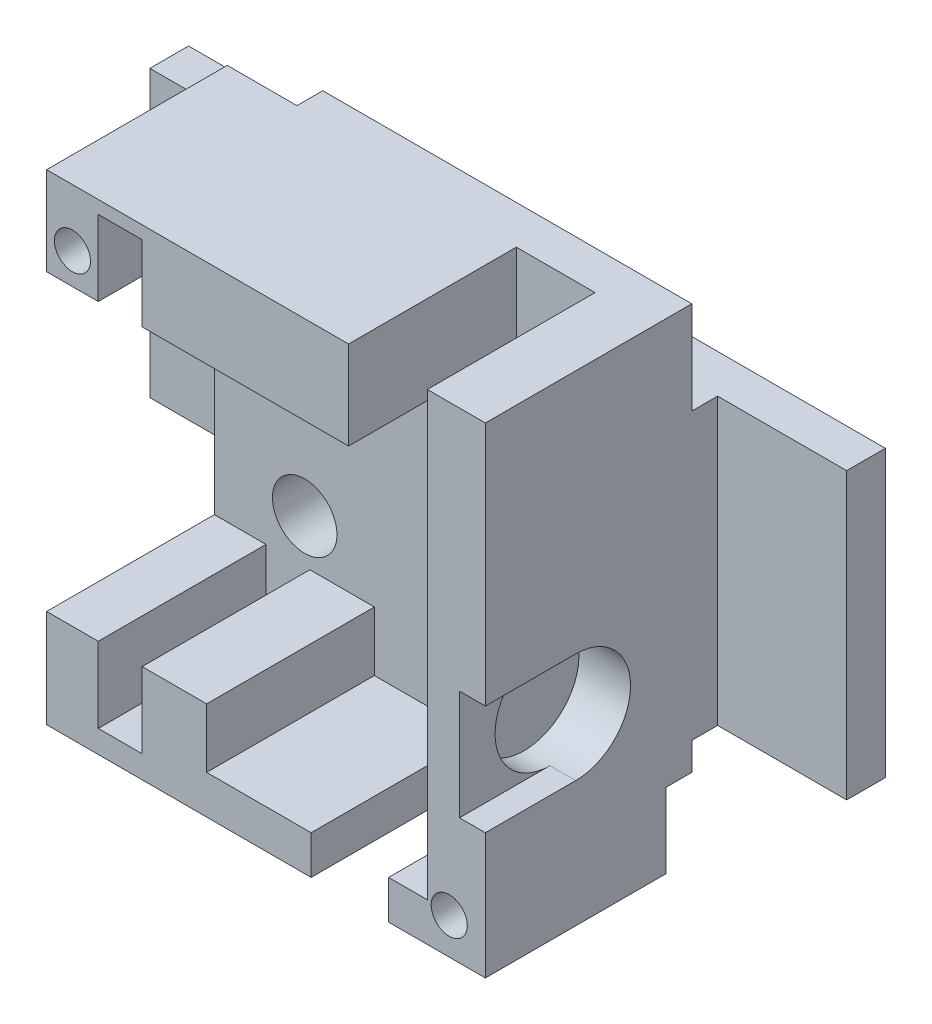
SolidWorks part; units mm, degrees
ref_plane "Front Plane" through (0, 0, 0) normal (0, 0, 1) x (1, 0, 0)
ref_plane "Top Plane" through (0, 0, 0) normal (0, 1, 0) x (1, 0, 0)
ref_plane "Right Plane" through (0, 0, 0) normal (1, 0, 0) x (0, 0, -1)
sketch "Sketch1" plane through (0, 0, 0) normal (0, 0, 1) x (1, 0, 0)
  line L1 (-17, 19) -> (17, 19)
  line L2 (-17, 19) -> (-17, -19)
  line L3 (-17, -19) -> (17, -19)
  line L4 (17, 19) -> (17, -19)
  line L5 (-17, 19) -> (17, -19) construction
  line L6 (-17, -19) -> (17, 19) construction
  point P0 (0, 0)
  dimension "D1" = 38
  dimension "D2" = 34
extrude "Boss-Extrude1" add sketch "Sketch1" along normal blind 16
sketch "Sketch2" plane through (0, 0, 16) normal (0, 0, 1) x (1, 0, 0)
  line L0 (0, 0) -> (-17, 0) construction
  line L5 (-17, 11.4) -> (5.4, 11.4)
  line L6 (-17, 11.4) -> (-17, -11.4)
  line L7 (-17, -11.4) -> (5.4, -11.4)
  line L8 (5.4, 11.4) -> (5.4, -11.4)
  line L9 (-17, 11.4) -> (5.4, -11.4) construction
  line L10 (-17, -11.4) -> (5.4, 11.4) construction
  line L11 (-17, 19) -> (-17, -19) construction
  line L12 (-10.6, -11.4) -> (-10.6, -16.25)
  line L13 (-13, 11.4) -> (-10.6, 11.4)
  line L14 (-13, 11.4) -> (-13, 16.25)
  line L15 (-13, 16.25) -> (-10.6, 16.25)
  line L16 (-10.6, 11.4) -> (-10.6, 16.25)
  line L17 (-13, -11.4) -> (-13, -16.25)
  line L18 (-13, -16.25) -> (-10.6, -16.25)
  line L21 (-17, -11.4) -> (-17, 4.4)
  point P0 (-5.8, 0)
  dimension "D1" = 22.4
  dimension "D2" = 22.8
  dimension "D3" = 5.8
  dimension "D4" = 4
  dimension "D5" = 2.4
  dimension "D6" = 4.85
extrude "Cut-Extrude1" cut sketch "Sketch2" against normal blind 13 contours L8 L5 L6 L7 | L17 L18 L12 L7 | L5 L16 L15 L14
sketch "Sketch3" plane through (0, 0, 16) normal (0, 0, 1) x (1, 0, 0)
  line L1 (5.4, -11.4) -> (-4.6, -11.4)
  line L2 (5.4, -11.4) -> (5.4, -16)
  line L3 (5.4, -16) -> (-4.6, -16)
  line L4 (-4.6, -11.4) -> (-4.6, -16)
  line L5 (5.4, -16) -> (8.4, -16)
  line L6 (5.4, -16) -> (5.4, -11.4)
  line L7 (5.4, -11.4) -> (8.4, -11.4)
  line L8 (8.4, -16) -> (8.4, -11.4)
  line L10 (-17, -19) -> (17, -19) construction
  line L11 (17, 19) -> (-17, 19) construction
  line L12 (8.4, -16) -> (11.4, -16)
  line L13 (8.4, -16) -> (8.4, 19)
  line L14 (8.4, 19) -> (11.4, 19)
  line L15 (11.4, -16) -> (11.4, 19)
  line M11 (17, 19) -> (-17, 19)
  line M21 (5.4, -11.4) -> (-10.6, -11.4)
  dimension "D1" = 3
  dimension "D2" = 10
  dimension "D3" = 3
  dimension "D4" = 3
extrude "Cut-Extrude2" cut sketch "Sketch3" against normal blind 13 contours L12 L15 L13 L8 M11 | L4 L3 L2 M21 | L5 L8 L7 L2
sketch "Sketch4" plane through (0, 0, 16) normal (0, 0, 1) x (1, 0, 0)
  line L0 (-17, 19) -> (-17, 11.4) construction
  line L3 (-17, -19) -> (17, -19) construction
  line L4 (17, -19) -> (17, 19) construction
  line L5 (8.4, 19) -> (-17, 19) construction
  circle A0 centre (-15, 13.8) radius 1.4
  circle A1 centre (14.2, -16.2) radius 1.4
  dimension "D2" = 5.2
  dimension "D3" = 2.8
  dimension "D4" = 2.8
  dimension "D5" = 2.8
  dimension "D6" = 2.8
  dimension "D1" = 2
extrude "Cut-Extrude3" cut sketch "Sketch4" against normal through all
sketch "Sketch5" plane through (0, 0, 0) normal (0, 0, -1) x (-1, 0, 0)
  line L0 (-17, 19) -> (17, 19) construction
  line L1 (18.4, 13.8) -> (11.6, 13.8)
  line L2 (18.4, 13.8) -> (18.4, 19)
  line L3 (18.4, 19) -> (11.6, 19)
  line L4 (11.6, 13.8) -> (11.6, 19)
  line L5 (-17, -19) -> (-17, 19) construction
  line L6 (-14.2, -19.2) -> (-17, -19.2)
  line L7 (-14.2, -19.2) -> (-14.2, -13.2)
  line L8 (-14.2, -13.2) -> (-17, -13.2)
  line L9 (-17, -19.2) -> (-17, -13.2)
  line L11 (-14.2, -19.2) -> (-10.2, -19.2)
  line L12 (-14.2, -19.2) -> (-14.2, -13.2)
  line L13 (-14.2, -13.2) -> (-10.2, -13.2)
  line L14 (-10.2, -19.2) -> (-10.2, -13.2)
  circle A0 centre (15, 13.8) radius 3.4
  circle A1 centre (-14.2, -16.2) radius 3
  circle M1 centre (15, 13.8) radius 1.4
  circle M2 centre (-14.2, -16.2) radius 1.4
  line M3 (-17, 19) -> (-17, -19)
  line M4 (-17, -19) -> (17, -19)
  line M5 (17, -19) -> (17, 19)
  line M6 (17, 19) -> (-17, 19)
  dimension "D1" = 6.8
  dimension "D2" = 6
  dimension "D3" = 4
extrude "Cut-Extrude5" cut sketch "Sketch5" against normal blind 2 contours A1 L7 M4 M2 | L7 A1 L9 M4 M2 | A1 M3 M4 | A1 L8 M3 | L9 A1 | A1 L7 M4 | A1 L9 L6 M4 | L7 A1 M4 | A0 L2 L3 M5 | A0 L4 M5 M6 | A0 L1 M5 M1 | L1 A0 M5 | A0 L1 M5 | L1 A0 M5 M1 | A1 L14 L13 M4
sketch "Sketch7" plane through (0, 19, 0) normal (0, 1, 0) x (1, 0, 0)
  line L0 (17, -16) -> (17, 0) construction
  line L1 (-17, -16) -> (17, -16)
  line L2 (-17, -16) -> (-17, -15)
  line L3 (-17, -15) -> (17, -15)
  line L4 (17, -16) -> (17, -15)
  dimension "D1" = 1
extrude "Cut-Extrude6" cut sketch "Sketch7" against normal through all
sketch "Sketch9" plane through (0, 0, 15) normal (0, 0, 1) x (1, 0, 0)
  line L0 (8.4, 19) -> (-17, 19) construction
  line L1 (-9, 19) -> (17, 19)
  line L2 (-9, 19) -> (-9, 12.5)
  line L3 (-9, 12.5) -> (17, 12.5)
  line L4 (17, 19) -> (17, 12.5)
  line L5 (17, -19) -> (17, 19) construction
  line L6 (-17, -19) -> (-17, -11.4) construction
  line L7 (-17, -12.4) -> (-14, -12.4)
  line L8 (-17, -12.4) -> (-17, -19)
  line L9 (-17, -19) -> (-14, -19)
  line L10 (-14, -12.4) -> (-14, -19)
  line L11 (17, -19) -> (-17, -19) construction
  line L12 (-13, -16.25) -> (-10.6, -16.25) construction
  line L13 (-8.6, -19) -> (-5.6, -19)
  line L14 (-8.6, -19) -> (-8.6, -12.4)
  line L15 (-8.6, -12.4) -> (-5.6, -12.4)
  line L16 (-5.6, -19) -> (-5.6, -12.4)
  line L17 (-5.6, -19) -> (11.4, -19)
  line L18 (-5.6, -19) -> (-5.6, -17)
  line L19 (-5.6, -17) -> (11.4, -17)
  line L20 (11.4, -19) -> (11.4, -17)
  line L21 (-14, -19) -> (-8.6, -19)
  line L22 (-14, -19) -> (-14, -18.25)
  line L23 (-10.6, -11.4) -> (-4.6, -11.4) construction
  line L24 (-17, -11.4) -> (-13, -11.4) construction
  line L25 (-10.6, -11.4) -> (-10.6, -16.25) construction
  line L26 (-4.6, -11.4) -> (-4.6, -16) construction
  line L27 (-4.6, -16) -> (11.4, -16) construction
  line L28 (-13, -11.4) -> (-13, -16.25) construction
  line L29 (-14, -18.25) -> (-8.6, -18.25)
  line L30 (-8.6, -19) -> (-8.6, -18.25)
  line L32 (-13, 16.25) -> (-10.6, 16.25) construction
  line L33 (-17, 19) -> (-9, 19)
  line L34 (-17, 19) -> (-17, 18.25)
  line L35 (-17, 18.25) -> (-9, 18.25)
  line L36 (-9, 19) -> (-9, 18.25)
  line L37 (11.4, -16) -> (11.4, 19) construction
  line L38 (17, 19) -> (13.4, 19)
  line L39 (17, 19) -> (17, 1)
  line L40 (17, 1) -> (13.4, 1)
  line L41 (13.4, 19) -> (13.4, 1)
  line M21 (8.4, -11.4) -> (8.4, 19)
  line M22 (8.4, 19) -> (-17, 19)
  line M23 (-17, 19) -> (-17, 11.4)
  dimension "D1" = 6.5
  dimension "D2" = 26
  dimension "D3" = 1
  dimension "D4" = 1
  dimension "D5" = 2
  dimension "D6" = 1
  dimension "D7" = 1
  dimension "D8" = 1
  dimension "D9" = 2
  dimension "D10" = 2
  dimension "D11" = 2
  dimension "D12" = 17
  dimension "D13" = 18
extrude "Cut-Extrude9" cut sketch "Sketch9" against normal through all contours L2 L3 M21 M22 | L35 L2 M23 M22 | L41 L1 L3 M21 | L1 L41 L3 L4 | L3 L41 L40 L39 | L17 L20 L19 L16 | L13 L16 L15 L14 | L29 L10 L21 L14 | L10 L7 L8 L9
sketch "Sketch10" plane through (0, 0, 3) normal (0, 0, 1) x (1, 0, 0)
  line L1 (-10, 8) -> (10, 8)
  line L2 (-10, 8) -> (-10, -8)
  line L3 (-10, -8) -> (10, -8)
  line L4 (10, 8) -> (10, -8)
  line L5 (-10, 8) -> (10, -8) construction
  line L6 (-10, -8) -> (10, 8) construction
  circle A0 centre (-10, 8) radius 2.5
  circle A1 centre (10, 8) radius 2.5
  circle A2 centre (-10, -8) radius 2.5
  circle A3 centre (10, -8) radius 2.5
  point P0 (0, 0)
  line M6 (8.4, 12.5) -> (8.4, -11.4)
  line M22 (11.4, -16) -> (11.4, 12.5)
  dimension "D3" = 5
  dimension "D1" = 20
  dimension "D2" = 16
extrude "Cut-Extrude10" cut sketch "Sketch10" against normal blind 2 and the other way through all contours L2 A0 L1 | L1 A0 L2 | A1 L4 L1 M6 | A1 L1 L4 M22 M6 | A1 M22 | A1 L1 M6 | L1 A1 M6 | L3 A2 L2 | L2 A2 L3 | A3 L4 L3 M22 M6 | A3 M22 | L4 A3 L3 M6 | A3 L3 M6 | L3 A3 M6
sketch "Sketch11" plane through (0, 0, 15) normal (0, 0, 1) x (1, 0, 0)
  line L5 (5.4, -11.4) -> (8.4, -11.4) construction
  line L6 (12.5, -8) -> (7.5, -8)
  line L7 (12.5, -8) -> (12.5, -11.4)
  line L8 (11.4, -11.4) -> (7.5, -11.4)
  line L9 (7.5, -8) -> (7.5, -11.4)
  line L10 (-9, 12.5) -> (8.4, 12.5) construction
  line L11 (12.5, 8) -> (7.5, 8)
  line L12 (12.5, 8) -> (12.5, 12.5)
  line L13 (12.5, 12.5) -> (7.5, 12.5)
  line L14 (7.5, 8) -> (7.5, 12.5)
  line L16 (11.4, -16) -> (12.5, -16)
  line L17 (11.4, -16) -> (11.4, -11.4)
  line L19 (12.5, -16) -> (12.5, -11.4)
  arc A0 (11.4, -10.0712) -> (11.4, -5.9288) centre (10, -8) ccw construction
  arc A1 (11.4, 5.9288) -> (11.4, 10.0712) centre (10, 8) ccw construction
extrude "Cut-Extrude11" cut sketch "Sketch11" against normal blind 12
sketch "Sketch12" plane through (0, 0, 15) normal (0, 0, 1) x (1, 0, 0)
  line L1 (-10.6, 11.4) -> (-9.6, 11.4)
  line L2 (-10.6, 11.4) -> (-10.6, 16.25)
  line L3 (-10.6, 16.25) -> (-9.6, 16.25)
  line L4 (-9.6, 11.4) -> (-9.6, 16.25)
  line L5 (-10.6, -11.4) -> (-9.6, -11.4)
  line L6 (-10.6, -11.4) -> (-10.6, -16.25)
  line L7 (-10.6, -16.25) -> (-9.6, -16.25)
  line L8 (-9.6, -11.4) -> (-9.6, -16.25)
  line L10 (5.4, -11.4) -> (6.4, -11.4)
  line L11 (5.4, -11.4) -> (5.4, 11.4)
  line L12 (5.4, 11.4) -> (6.4, 11.4)
  line L13 (6.4, -11.4) -> (6.4, 11.4)
  dimension "D1" = 1
  dimension "D2" = 1
  dimension "D3" = 4.85
  dimension "D4" = 4.85
  dimension "D5" = 1
extrude "Cut-Extrude12" cut sketch "Sketch12" against normal blind 12
sketch "Sketch14" plane through (17, 0, 0) normal (1, 0, 0) x (0, 0, -1)
  line L0 (-15, -19) -> (-15, 1) construction
  line L1 (-15, -19) -> (-2, -19) construction
  circle A0 centre (-9, -5) radius 4.25
  dimension "D1" = 8.5
  dimension "D2" = 6
  dimension "D3" = 14
extrude "Cut-Extrude13" cut sketch "Sketch14" against normal blind 4
sketch "Sketch17" plane through (0, 0, 15) normal (0, 0, 1) x (1, 0, 0)
  line L1 (-13, 16.25) -> (-9.6, 16.25)
  line L2 (-13, 16.25) -> (-13, 17.25)
  line L3 (-13, 17.25) -> (-9.6, 17.25)
  line L4 (-9.6, 16.25) -> (-9.6, 17.25)
  line L7 (-9.6, -16.25) -> (-13, -16.25)
  line L8 (-9.6, -16.25) -> (-9.6, -17.25)
  line L9 (-9.6, -17.25) -> (-13, -17.25)
  line L10 (-13, -16.25) -> (-13, -17.25)
  dimension "D1" = 1
  dimension "D2" = 3.4
  dimension "D3" = 1
  dimension "D4" = 3.4
extrude "Cut-Extrude16" cut sketch "Sketch17" against normal blind 12
sketch "Sketch18" plane through (0, 0, 1) normal (0, 0, 1) x (1, 0, 0)
  circle A1 centre (-10, 8) radius 1.4
  circle A2 centre (10, 8) radius 1.4
  circle A3 centre (-10, -8) radius 1.4
  circle A4 centre (10, -8) radius 1.4
  dimension "D1" = 2.8
  dimension "D2" = 2.8
  dimension "D3" = 2.8
  dimension "D4" = 2.8
extrude "Cut-Extrude17" cut sketch "Sketch18" against normal blind 12
sketch "Sketch19" plane through (0, 0, 0) normal (0, 0, 1) x (1, 0, 0)
  line L1 (-17, 18.25) -> (17, 18.25)
  line L2 (-17, 18.25) -> (-17, -19)
  line L3 (-17, -19) -> (17, -19)
  line L4 (17, 18.25) -> (17, -19)
  line L5 (-9, 18.25) -> (17, 18.25)
  line L6 (-9, 18.25) -> (-9, 12.4767)
  line L7 (-9, 12.4767) -> (17, 12.4767)
  line L8 (17, 18.25) -> (17, 12.4767)
  line L9 (17, 12.4767) -> (13.4, 12.4767)
  line L10 (17, 12.4767) -> (17, 1)
  line L11 (17, 1) -> (13.4, 1)
  line L12 (13.4, 12.4767) -> (13.4, 1)
  line L13 (-17, -12.4) -> (-14, -12.4)
  line L14 (-17, -12.4) -> (-17, -19)
  line L15 (-17, -19) -> (-14, -19)
  line L16 (-14, -12.4) -> (-14, -19)
  line L17 (-14, -19) -> (-8.6, -19)
  line L18 (-14, -19) -> (-14, -18.25)
  line L19 (-14, -18.25) -> (-8.6, -18.25)
  line L20 (-8.6, -19) -> (-8.6, -18.25)
  line L21 (-8.6, -12.4) -> (-5.6, -12.4)
  line L22 (-8.6, -12.4) -> (-8.6, -19)
  line L23 (-8.6, -19) -> (-5.6, -19)
  line L24 (-5.6, -12.4) -> (-5.6, -19)
  line L25 (-5.6, -17) -> (11.4, -17)
  line L26 (-5.6, -17) -> (-5.6, -19)
  line L27 (-5.6, -19) -> (11.4, -19)
  line L28 (11.4, -17) -> (11.4, -19)
extrude "Boss-Extrude2" add sketch "Sketch19" along normal blind 16 contours L6 L7 L4 L1 | L7 L12 L11 L4 | L24 L21 L22 L20 L3 | L16 L13 L2 L3 | L3 L20 L19 L16 | L28 L25 L24 L3
sketch "Sketch20" plane through (0, 0, 15) normal (0, 0, 1) x (1, 0, 0)
  line L0 (-9.6, 11.4) -> (6.4, 11.4) construction
  line L1 (-17, 18.25) -> (17, 18.25)
  line L2 (-17, 18.25) -> (-17, -19)
  line L3 (-17, -19) -> (17, -19)
  line L4 (17, 18.25) -> (17, -19)
  line L5 (-13, 11.4) -> (-17, 11.4)
  line L6 (-13, 11.4) -> (-13, 18.25)
  line L7 (-13, 18.25) -> (-17, 18.25)
  line L8 (-17, 11.4) -> (-17, 18.25)
  line L9 (-13, 18.25) -> (-9.6, 18.25)
  line L10 (-13, 18.25) -> (-13, 17.25)
  line L11 (-13, 17.25) -> (-9.6, 17.25)
  line L12 (-9.6, 18.25) -> (-9.6, 17.25)
  line L13 (-9.6, 18.25) -> (-9, 18.25)
  line L14 (-9.6, 18.25) -> (-9.6, 11.4)
  line L15 (-9.6, 11.4) -> (-9, 11.4)
  line L16 (-9, 18.25) -> (-9, 11.4)
  line L17 (-17, -11.4) -> (-13, -11.4)
  line L18 (-9, 11.4) -> (7.5, 11.4)
  line L19 (-9, 11.4) -> (-9, 12.4767)
  line L20 (-9, 12.4767) -> (7.5, 12.4767)
  line L21 (7.5, 11.4) -> (7.5, 12.4767)
  line L22 (7.5, -11.4) -> (6.4, -11.4)
  line L23 (7.5, -11.4) -> (7.5, 11.4)
  line L24 (7.5, 11.4) -> (6.4, 11.4)
  line L25 (6.4, -11.4) -> (6.4, 11.4)
  line L26 (17, -19) -> (13.4, -19)
  line L27 (17, -19) -> (17, 1)
  line L28 (17, 1) -> (13.4, 1)
  line L30 (-13, -11.4) -> (-13, -17.25)
  line L31 (-13, -17.25) -> (-9.6, -17.25)
  line L32 (-9.6, -17.25) -> (-9.6, -11.4)
  line L33 (-9.6, -11.4) -> (-4.6, -11.4)
  line L34 (-4.6, -11.4) -> (-4.6, -16)
  line L35 (-4.6, -16) -> (12.5, -16)
  line L36 (12.5, -16) -> (12.5, 12.4767)
  line L37 (12.5, 12.4767) -> (13.4, 12.4767)
  line L38 (13.4, 12.4767) -> (13.4, 1)
  line L39 (-17, -12.4) -> (-14, -12.4)
  line L40 (-14, -12.4) -> (-14, -18.25)
  line L41 (-14, -18.25) -> (-8.6, -18.25)
  line L42 (-8.6, -18.25) -> (-8.6, -12.4)
  line L43 (-8.6, -12.4) -> (-5.6, -12.4)
  line L44 (-5.6, -12.4) -> (-5.6, -17)
  line L45 (-5.6, -17) -> (11.4, -17)
  line L46 (11.4, -17) -> (11.4, -19)
  line L47 (11.4, -19) -> (17, -19)
  circle A0 centre (-15, 13.8) radius 1.4
  circle A1 centre (14.2, -16.2) radius 1.4
  circle M5 centre (-15, 13.8) radius 1.4
  line M6 (7.5, 12.4767) -> (-9, 12.4767)
  line M7 (-9, 12.4767) -> (-9, 18.25)
  line M8 (-9, 18.25) -> (-17, 18.25)
  line M9 (-17, 18.25) -> (-17, 11.4)
  line M10 (-17, 11.4) -> (-13, 11.4)
  line M11 (-13, 11.4) -> (-13, 17.25)
  line M12 (-13, 17.25) -> (-9.6, 17.25)
  line M13 (-9.6, 17.25) -> (-9.6, 11.4)
  line M14 (-9.6, 11.4) -> (6.4, 11.4)
  line M15 (6.4, 11.4) -> (6.4, -11.4)
  line M16 (6.4, -11.4) -> (7.5, -11.4)
  line M17 (7.5, -11.4) -> (7.5, -8)
  line M21 (7.5, 8) -> (7.5, 12.4767)
extrude "Boss-Extrude3" add sketch "Sketch20" along normal blind 1 contours L6 L1 M11 M9 M10 M5 | L12 L1 L6 M12 | L16 L12 M7 M8 M13 M14 | L18 L16 M14 M21 M6 | L23 L18 M17 M21 M15 M16 | L45 L46 L3 L4 L28 L38 L37 L36 L35 L34 L33 L32 L31 L30 L17 L2 L39 L40 L41 L42 L43 L44 A1
sketch "Sketch21" plane through (0, 0, 16) normal (0, 0, 1) x (1, 0, 0)
  line L0 (12.5, -16) -> (12.5, -8) construction
  line L1 (7.5, 12.4767) -> (6.4, 12.4767)
  line L2 (7.5, 12.4767) -> (7.5, -11.4)
  line L3 (7.5, -11.4) -> (6.4, -11.4)
  line L4 (6.4, 12.4767) -> (6.4, -11.4)
  line L5 (7.5, 12.4767) -> (12.5, 12.4767)
  line L6 (7.5, 12.4767) -> (7.5, -11.4)
  line L7 (7.5, -11.4) -> (12.5, -11.4)
  line L8 (12.5, 12.4767) -> (12.5, -11.4)
  line M13 (6.4, 11.4) -> (6.4, -11.4)
  line M14 (6.4, -11.4) -> (7.5, -11.4)
  line M15 (7.5, -11.4) -> (7.5, 12.4767)
  line M16 (7.5, 12.4767) -> (12.5, 12.4767)
  line M17 (12.5, 12.4767) -> (12.5, -16)
extrude "Cut-Extrude18" cut sketch "Sketch21" against normal blind 13 contours L7 M15 M17 M16 | L1 L4 M13 M14 M15
sketch "Sketch22" plane through (-17, 0, 0) normal (-1, 0, 0) x (0, 0, 1)
  line L0 (3, -11.4) -> (16, -11.4) construction
  line L1 (16, 18.25) -> (0, 18.25)
  line L2 (16, 18.25) -> (16, -19)
  line L3 (16, -19) -> (0, -19)
  line L4 (0, 18.25) -> (0, -19)
  line L5 (0, 11.0505) -> (3, 11.0505)
  line L6 (0, 11.0505) -> (0, -11.4)
  line L7 (0, -11.4) -> (3, -11.4)
  line L8 (3, 11.0505) -> (3, -11.4)
  line L9 (3, 11.4) -> (3, -11.4) construction
  line M3 (3, -11.4) -> (3, 11.4)
  line M8 (2, 11.0505) -> (0, 11.0505)
  line M9 (0, 11.0505) -> (0, -19)
extrude "Boss-Extrude4" add sketch "Sketch22" along normal blind 10 contours L7 L5 M9 M3 M8
ref_plane "Plane1" through (0, 0, 0) normal (1, 0, 0) x (0, 0, -1)
mirror "Mirror1" about plane through (0, 0, 0) normal (1, 0, 0) of "Boss-Extrude4"
sketch "Sketch23" plane through (0, 0, 16) normal (0, 0, 1) x (1, 0, 0)
  line L0 (-17, 18.25) -> (17, 18.25) construction
  line L1 (6.4, 11.4) -> (12.5, 11.4)
  line L2 (6.4, 11.4) -> (6.4, 18.25)
  line L3 (6.4, 18.25) -> (12.5, 18.25)
  line L4 (12.5, 11.4) -> (12.5, 18.25)
extrude "Cut-Extrude19" cut sketch "Sketch23" against normal blind 13
sketch "Sketch24" plane through (0, 0, 3) normal (0, 0, 1) x (1, 0, 0)
  line L1 (17, -19) -> (27, -19)
  line L2 (17, -19) -> (17, -11.4)
  line L3 (17, -11.4) -> (27, -11.4)
  line L4 (27, -19) -> (27, -11.4)
  line L5 (27, 11.0505) -> (17, 11.0505)
  line L6 (27, 11.0505) -> (27, 18.25)
  line L7 (27, 18.25) -> (17, 18.25)
  line L8 (17, 11.0505) -> (17, 18.25)
  line L9 (-27, 11.0505) -> (-17, 11.0505)
  line L10 (-27, 11.0505) -> (-27, 18.25)
  line L11 (-27, 18.25) -> (-17, 18.25)
  line L12 (-17, 11.0505) -> (-17, 18.25)
  line L13 (-27, -11.4) -> (-17, -11.4)
  line L14 (-27, -11.4) -> (-27, -19)
  line L15 (-27, -19) -> (-17, -19)
  line L16 (-17, -11.4) -> (-17, -19)
sketch "Sketch26" plane through (0, 0, 0) normal (0, 0, -1) x (-1, 0, 0)
  line L1 (-10.2, -17) -> (-11.4, -17)
  line L2 (-10.2, -17) -> (-10.2, -19)
  line L3 (-10.2, -19) -> (-11.4, -19)
  line L4 (-11.4, -17) -> (-11.4, -19)
extrude "Cut-Extrude21" cut sketch "Sketch26" against normal blind 2
sketch "Sketch27" plane through (0, 0, 0) normal (0, 0, -1) x (-1, 0, 0)
  line L1 (27, -11.0505) -> (-27, -11.0505)
  line L2 (27, -11.0505) -> (27, 11.0505)
  line L3 (27, 11.0505) -> (-27, 11.0505)
  line L4 (-27, -11.0505) -> (-27, 11.0505)
  line L5 (27, -11.0505) -> (-27, 11.0505) construction
  line L6 (27, 11.0505) -> (-27, -11.0505) construction
  circle A0 centre (-10, 8) radius 1.4
  circle A1 centre (-10, -8) radius 1.4
  circle A2 centre (10, -8) radius 1.4
  circle A3 centre (10, 8) radius 1.4
  point P0 (0, 0)
extrude "Boss-Extrude6" add sketch "Sketch27" along normal blind 5
sketch "Sketch28" plane through (0, 0, 3) normal (0, 0, 1) x (1, 0, 0)
  line L5 (-27, 11.0505) -> (-17, 11.0505)
  line L6 (-27, 11.0505) -> (-27, -11.4)
  line L11 (-27, -11.4) -> (-17, -11.4)
  line L12 (-17, 11.0505) -> (-17, -11.4)
  line L13 (17, -11.4) -> (27, -11.4)
  line L14 (17, -11.4) -> (17, 11.0505)
  line L15 (17, 11.0505) -> (27, 11.0505)
  line L16 (27, -11.4) -> (27, 11.0505)
extrude "Cut-Extrude22" cut sketch "Sketch28" against normal blind 5
sketch "Sketch29" plane through (0, 0, 2) normal (0, 0, -1) x (-1, 0, 0)
  circle A0 centre (15, 13.8) radius 1.4
  circle A1 centre (15, 13.8) radius 3.4
extrude "Cut-Extrude23" cut sketch "Sketch29" along normal blind 7
sketch "Sketch30" plane through (0, 0, 1) normal (0, 0, 1) x (1, 0, 0)
  circle A0 centre (-10, 8) radius 2.5
  circle A1 centre (-10, 8) radius 1.4
  circle A2 centre (-10, -8) radius 2.5
  circle A3 centre (-10, -8) radius 1.4
  circle A4 centre (10, -8) radius 1.4
  circle A5 centre (10, -8) radius 2.5
  circle A6 centre (10, 8) radius 1.4
  circle A7 centre (10, 8) radius 2.5
extrude "Cut-Extrude24" cut sketch "Sketch30" against normal blind 3
sketch "Sketch31" plane through (0, 0, 16) normal (0, 0, 1) x (1, 0, 0)
  line L0 (-17, -19) -> (17, -19) construction
  line L1 (9.5, -19) -> (3.5, -19)
  line L2 (9.5, -19) -> (9.5, -16)
  line L3 (9.5, -16) -> (3.5, -16)
  line L4 (3.5, -19) -> (3.5, -16)
  line L5 (-4.6, -16) -> (12.5, -16) construction
  line L6 (12.5, -16) -> (12.5, -8) construction
  dimension "D1" = 3
  dimension "D2" = 6
extrude "Cut-Extrude25" cut sketch "Sketch31" against normal blind 13
sketch "Sketch32" plane through (17, 0, 0) normal (1, 0, 0) x (0, 0, -1)
  line L0 (-16, 18.25) -> (-16, -19) construction
  line L1 (-9, -0.75) -> (-16, -0.75)
  line L2 (-9, -0.75) -> (-9, -9.25)
  line L3 (-9, -9.25) -> (-16, -9.25)
  line L4 (-16, -0.75) -> (-16, -9.25)
  circle A0 centre (-9, -5) radius 4.25 construction
  circle A1 centre (-9, -5) radius 4.25 construction
extrude "Cut-Extrude26" cut sketch "Sketch32" against normal blind 2
